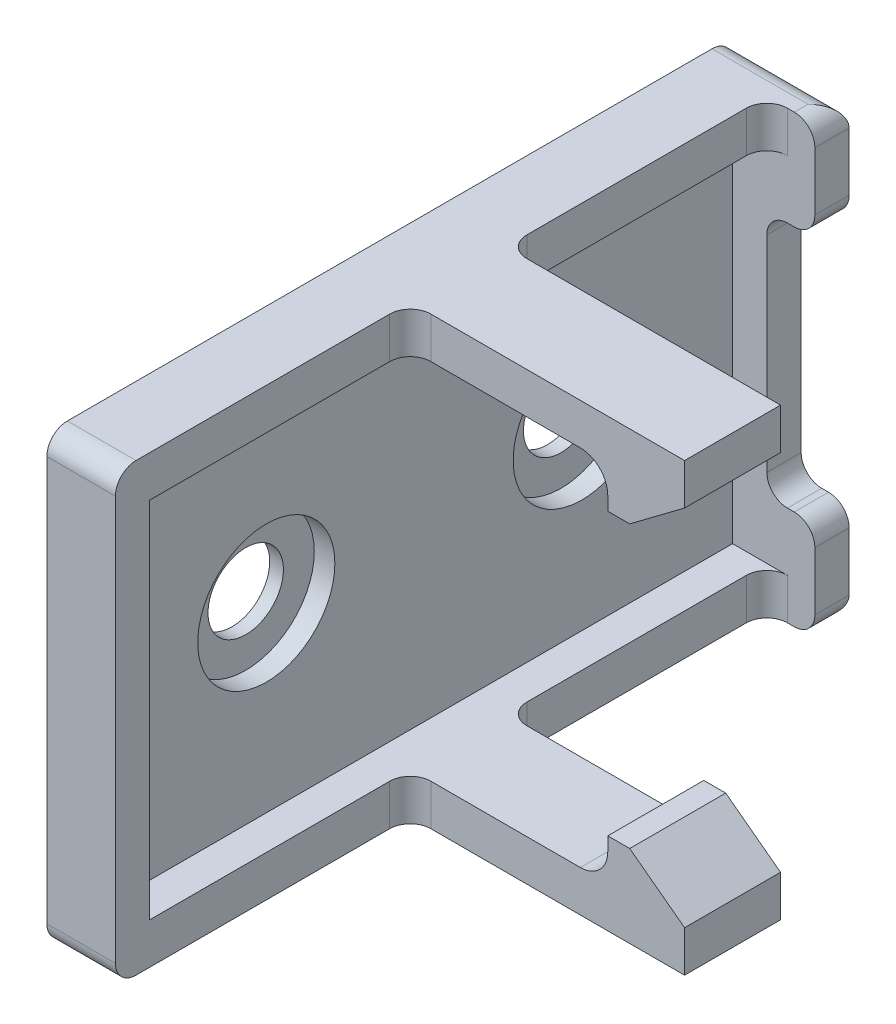
SolidWorks part; units mm, degrees
ref_plane "Front Plane" through (0, 0, 0) normal (0, 0, 1) x (1, 0, 0)
ref_plane "Top Plane" through (0, 0, 0) normal (0, 1, 0) x (1, 0, 0)
ref_plane "Right Plane" through (0, 0, 0) normal (1, 0, 0) x (0, 0, -1)
sketch "Sketch1" plane through (0, 0, 0) normal (0, 0, 1) x (1, 0, 0)
  line L1 (0, 22.5) -> (0, -22.5) construction
  line L8 (-20, 0) -> (20, 0) construction
  line L16 (-1.25, 16.25) -> (-1.25, -16.25)
  line L17 (1.25, 16.25) -> (1.25, -16.25)
  line L18 (1.25, -16.25) -> (-1.25, -16.25)
  line L19 (1.25, 16.25) -> (-1.25, 16.25)
  point P0 (1.25, 0)
  point P1 (0, 0)
  point P2 (0, -16.25)
  point P3 (0, 16.25)
  dimension "D1" = 32.5
  dimension "D2" = 2.5
extrude "Boss-Extrude1" add sketch "Sketch1" along normal blind 50
sketch "Sketch5" plane through (-1.25, 0, 0) normal (-1, 0, 0) x (0, 0, 1)
  line L0 (13.5, 0) -> (36.5, 0) construction
  line L1 (25, 0) -> (25, 10.1767) construction
  line L2 (50, 16.25) -> (50, -16.25) construction
  line L3 (25, 16.25) -> (25, -16.25) construction
  line L4 (50, 16.25) -> (0, 16.25) construction
  line L5 (50, -16.25) -> (0, -16.25) construction
  circle A0 centre (13.5, 0) radius 2.75
  circle A1 centre (36.5, 0) radius 2.75
  point P10 (50, 0)
  dimension "D1" = 5.5
  dimension "D2" = 5.5
  dimension "D3" = 23
extrude "Cut-Extrude5" cut sketch "Sketch5" against normal blind 30.5
sketch "Sketch6" plane through (1.25, 0, 0) normal (1, 0, 0) x (0, 0, -1)
  circle A0 centre (-36.5, 0) radius 5
  circle A1 centre (-13.5, 0) radius 5
  dimension "D1" = 10
  dimension "D2" = 10
extrude "Cut-Extrude6" cut sketch "Sketch6" against normal blind 1.5
sketch "Sketch7" plane through (1.25, 0, 0) normal (1, 0, 0) x (0, 0, -1)
  line L0 (-25, 0) -> (-25, 16.25) construction
  line L1 (-47.5, 13.25) -> (-2.5, 13.25)
  line L2 (-47.5, 13.25) -> (-47.5, -13.25)
  line L3 (-47.5, -13.25) -> (-2.5, -13.25)
  line L4 (-2.5, 13.25) -> (-2.5, -13.25)
  line L5 (-47.5, 13.25) -> (-2.5, -13.25) construction
  line L6 (-47.5, -13.25) -> (-2.5, 13.25) construction
  line L7 (-50, 16.25) -> (0, 16.25)
  line L8 (-50, 16.25) -> (-50, -16.25)
  line L9 (-50, -16.25) -> (0, -16.25)
  line L10 (0, 16.25) -> (0, -16.25)
  line L11 (-50, 16.25) -> (0, -16.25) construction
  line L12 (-50, -16.25) -> (0, 16.25) construction
  line L13 (-50, 16.25) -> (0, 16.25) construction
  line L14 (-50, 0) -> (-25, 0) construction
  line L15 (-50, -16.25) -> (-50, 16.25) construction
  point P0 (-25, 0)
  point P5 (-25, 0)
  dimension "D1" = 45
  dimension "D4" = 26.5
extrude "Boss-Extrude2" add sketch "Sketch7" along normal blind 2.5
sketch "Sketch8" plane through (3.75, 0, 0) normal (1, 0, 0) x (0, 0, -1)
  line L0 (-25, 16.25) -> (-25, -16.25) construction
  line L1 (0, 16.25) -> (-50, 16.25) construction
  line L2 (-50, -16.25) -> (0, -16.25) construction
  line L4 (-28.5, 16.25) -> (-21.5, 16.25)
  line L5 (-28.5, 16.25) -> (-28.5, 10.25)
  line L6 (-28.5, 10.25) -> (-21.5, 10.25)
  line L7 (-21.5, 16.25) -> (-21.5, 10.25)
  line L8 (-28.5, 16.25) -> (-21.5, 10.25) construction
  line L9 (-28.5, 10.25) -> (-21.5, 16.25) construction
  line L10 (-2.5, 13.25) -> (-47.5, 13.25) construction
  line L11 (-50, 0) -> (0, 0) construction
  line L12 (-50, 16.25) -> (-50, -16.25) construction
  line L13 (0, -16.25) -> (0, 16.25) construction
  line L14 (-28.5, -10.25) -> (-21.5, -16.25) construction
  line L15 (-28.5, -16.25) -> (-21.5, -10.25) construction
  line L16 (-21.5, -16.25) -> (-21.5, -10.25)
  line L17 (-28.5, -10.25) -> (-21.5, -10.25)
  line L18 (-28.5, -16.25) -> (-28.5, -10.25)
  line L19 (-28.5, -16.25) -> (-21.5, -16.25)
  point P6 (-25, 13.25)
  point P23 (-25, -13.25)
  dimension "D1" = 7
extrude "Boss-Extrude3" add sketch "Sketch8" along normal blind 20
sketch "Sketch9" plane through (0, 0, 21.5) normal (0, 0, -1) x (-1, 0, 0)
  line L0 (-3.75, 13.25) -> (-16.15, 13.25)
  line L1 (-18.15, 11.25) -> (-18.15, 10.25)
  line L2 (-23.75, 10.25) -> (-3.75, 10.25) construction
  line L3 (-18.15, 10.25) -> (-3.75, 10.25)
  line L4 (-3.75, 10.25) -> (-3.75, 13.25)
  line L5 (1.25, 0) -> (-25.7071, 0) construction
  line L6 (1.25, 16.25) -> (1.25, -16.25) construction
  line L7 (-3.75, -10.25) -> (-3.75, -13.25)
  line L8 (-18.15, -10.25) -> (-3.75, -10.25)
  line L9 (-18.15, -11.25) -> (-18.15, -10.25)
  line L10 (-3.75, -13.25) -> (-16.15, -13.25)
  line L11 (-23.75, 13.25) -> (-19.75, 10.25)
  line L12 (-23.75, 10.25) -> (-23.75, 16.25) construction
  line L13 (-19.75, 10.25) -> (-23.75, 10.25)
  line L14 (-23.75, 10.25) -> (-23.75, 13.25)
  line L15 (-23.75, -10.25) -> (-23.75, -13.25)
  line L16 (-19.75, -10.25) -> (-23.75, -10.25)
  line L17 (-23.75, -13.25) -> (-19.75, -10.25)
  arc A0 (-16.15, -13.25) -> (-18.15, -11.25) centre (-16.15, -11.25) cw
  arc A1 (-18.15, 11.25) -> (-16.15, 13.25) centre (-16.15, 11.25) cw
  point P28 (-18.15, -13.25)
  point P31 (-18.15, 13.25)
  dimension "D3" = 2
  dimension "D1" = 14.4
  dimension "D2" = 5
extrude "Cut-Extrude9" cut sketch "Sketch9" against normal blind 20
sketch "Sketch10" plane through (0, 0, 2.5) normal (0, 0, 1) x (1, 0, 0)
  line L10 (0, 0) -> (5, 0) construction
  line L11 (7.25, -16.25) -> (7.25, -9)
  line L12 (3.75, 16.25) -> (7.25, 16.25)
  line L13 (3.75, 16.25) -> (3.75, 9)
  line L14 (3.75, 9) -> (7.25, 9)
  line L15 (7.25, 16.25) -> (7.25, 9)
  line L16 (3.75, -9) -> (7.25, -9)
  line L17 (3.75, -16.25) -> (3.75, -9)
  line L18 (3.75, -16.25) -> (7.25, -16.25)
  dimension "D1" = 9
  dimension "D2" = 3.5
extrude "Boss-Extrude4" add sketch "Sketch10" against normal up to surface (2.5 mm away) up to face at (1.25, 0, 0)
fillet "Fillet1" radius 1.5 16 edges at (3, -16.25, 0) (3, 16.25, 0) (1.25, 16.25, 50) (1.25, -16.25, 50) (3.75, -14.75, 28.5) (3.75, 14.75, 28.5) (3.75, 14.75, 21.5) (3.75, -14.75, 21.5) (7.25, -16.25, 1.25) (3.75, -14.75, 2.5) (3.75, 14.75, 2.5) (7.25, 16.25, 1.25) (7.25, -9, 1.25) (3.75, -9, 1.25) (7.25, 9, 1.25) (3.75, 9, 1.25)
